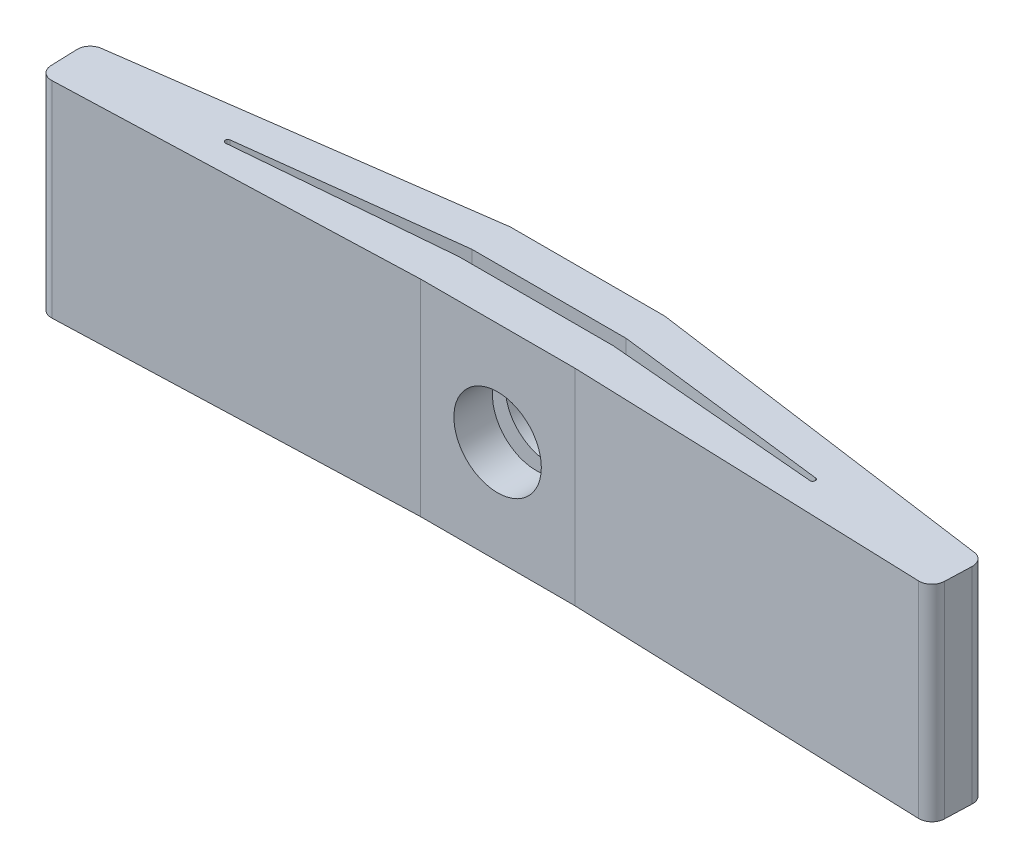
SolidWorks part; units mm, degrees
ref_plane "Front Plane" through (0, 0, 0) normal (0, 0, 1) x (1, 0, 0)
ref_plane "Top Plane" through (0, 0, 0) normal (0, 1, 0) x (1, 0, 0)
ref_plane "Right Plane" through (0, 0, 0) normal (1, 0, 0) x (0, 0, -1)
ref_plane "Plane1" through (0, 8, 0) normal (0, 1, 0) x (1, 0, 0)
sketch "Sketch1" plane through (0, 8, 0) normal (0, 1, 0) x (1, 0, 0)
  line L0 (34.7697, 2) -> (20.35, 4)
  line L1 (20.35, 4) -> (14.35, 4)
  line L2 (14.35, 4) -> (-0.0697, 2)
  line L3 (-0.0697, 2) -> (0, 0)
  line L4 (0, 0) -> (14.35, 0.5)
  line L5 (14.35, 0.5) -> (20.35, 0.5)
  line L6 (20.35, 0.5) -> (34.7, 0)
  line L7 (34.7, 0) -> (34.7697, 2)
extrude "Boss-Extrude1" add sketch "Sketch1" against normal blind 8
sketch "Sketch2" plane through (0, 0, 0) normal (0, -1, 0) x (1, 0, 0)
  line L0 (5.9688, -1.4823) -> (14.35, -2.5)
  line L1 (14.35, -2.5) -> (20.35, -2.5)
  line L2 (20.35, -2.5) -> (28.7312, -1.4823)
  line L3 (28.7106, -1.2834) -> (20.35, -2)
  line L4 (20.35, -2) -> (14.35, -2)
  line L5 (14.35, -2) -> (5.9894, -1.2834)
  arc A0 (28.7312, -1.4823) -> (28.7106, -1.2834) centre (28.7192, -1.383) ccw
  arc A1 (5.9894, -1.2834) -> (5.9688, -1.4823) centre (5.9808, -1.383) ccw
extrude "Cut-Extrude1" cut sketch "Sketch2" against normal through all
hole_wizard "M3 Clearance Hole1" positions "Sketch6" profile "Sketch5" hole size "M3" standard "ANSI Metric" end condition through all
sketch "Sketch6" plane through (0, 0, -0.5) normal (0, 0, 1) x (1, 0, 0)
  point P0 (17.35, 4)
sketch "Sketch5" plane through (17.35, 4, -0.5) normal (1, 0, 0) x (0, -1, 0)
  line L0 (0, 0) -> (0, 3.5)
  line L1 (0, 3.5) -> (1.7, 3.5)
  line L2 (1.7, 3.5) -> (1.7, 0)
  line L5 (1.7, 0) -> (0, 0)
  line L11 (0, -6.35) -> (0, 107.95) construction
  dimension "Thru Hole Dia." = 3.4
  dimension "Thru Hole Depth" = 3.5
fillet "Fillet1" radius 0.5 4 edges at (-0.0697, 4, -2) (34.7697, 4, -2) (34.7, 4, 0) (0, 4, 0)
